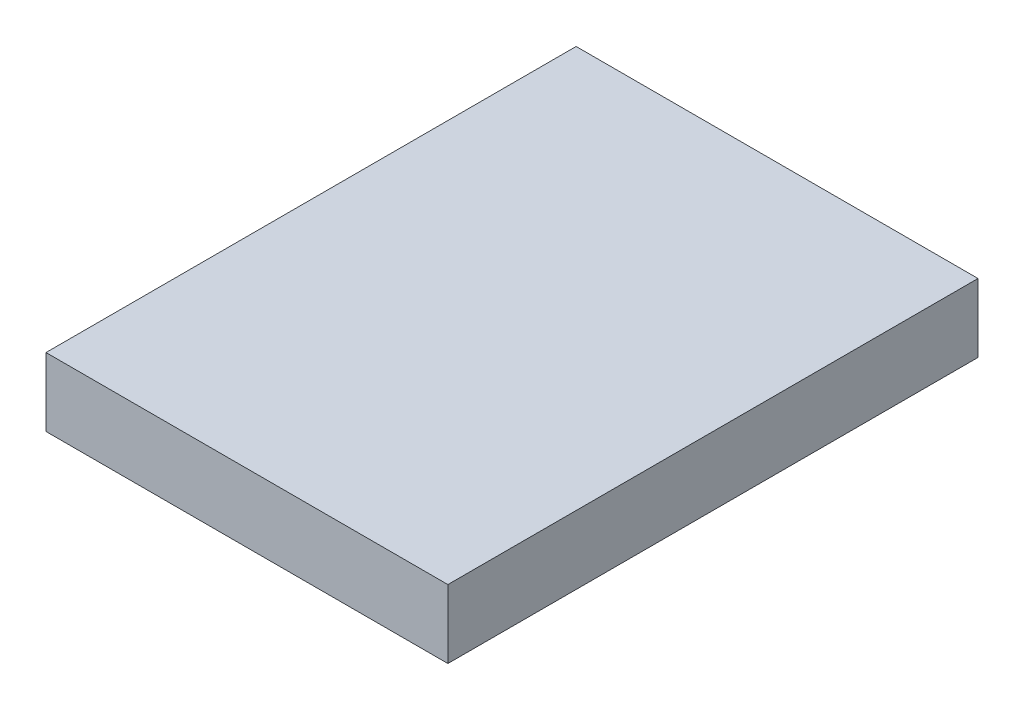
SolidWorks part; units mm, degrees
ref_plane "Front Plane" through (0, 0, 0) normal (0, 0, 1) x (1, 0, 0)
ref_plane "Top Plane" through (0, 0, 0) normal (0, 1, 0) x (1, 0, 0)
ref_plane "Right Plane" through (0, 0, 0) normal (1, 0, 0) x (0, 0, -1)
sketch "Sketch1" plane through (0, 0, 0) normal (0, 1, 0) x (1, 0, 0)
  line L0 (0, 0) -> (47, 0)
  line L1 (0, 0) -> (0, 62)
  line L2 (47, 0) -> (47, 62)
  line L3 (0, 62) -> (47, 62)
extrude "Boss-Extrude1" add sketch "Sketch1" along normal blind 8
